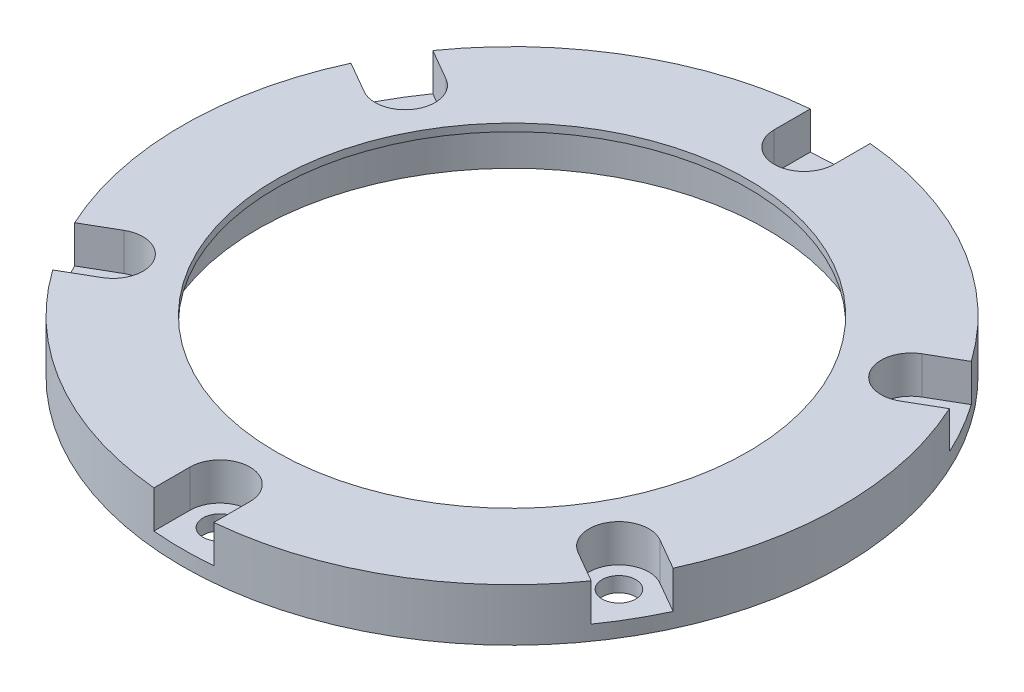
SolidWorks part; units mm, degrees
material "7075-T6, 플레이트 (SS)"
ref_plane "정면" through (0, 0, 0) normal (0, 0, 1) x (1, 0, 0)
ref_plane "윗면" through (0, 0, 0) normal (0, 1, 0) x (1, 0, 0)
ref_plane "우측면" through (0, 0, 0) normal (1, 0, 0) x (0, 0, -1)
sketch "스케치1" plane through (0, 0, 0) normal (0, 1, 0) x (1, 0, 0)
  circle A0 centre (0, 0) radius 44
  circle A1 centre (0, 0) radius 34
  dimension "D1" = 88
  dimension "D2" = 68
extrude "보스-돌출1" add sketch "스케치1" along normal blind 6
sketch "스케치2" plane through (0, 6, 0) normal (0, 1, 0) x (1, 0, 0)
  circle A0 centre (0, 0) radius 31.5
  circle A1 centre (0, 0) radius 44 construction
  circle A2 centre (0, 0) radius 44
  dimension "D1" = 63
extrude "보스-돌출2" add sketch "스케치2" along normal blind 1
sketch "스케치3" plane through (0, 7, 0) normal (0, 1, 0) x (1, 0, 0)
  circle A0 centre (0, 0) radius 39 construction
  point P3 (0, 39)
  dimension "D1" = 78
hole_wizard "M4 육각 소켓 머리 캡 나사용 카운터보어1" positions "스케치4" profile "스케치6" counterbore size "M4" standard "ISO" end condition through all
sketch "스케치4" plane through (0, 7, 0) normal (0, 1, 0) x (1, 0, 0)
  point P0 (0, 39)
sketch "스케치6" plane through (0, 7, -39) normal (1, 0, 0) x (0, 0, 1)
  line L0 (0, 0) -> (0, 7)
  line L1 (0, 7) -> (2.25, 7)
  line L3 (2.25, 7) -> (2.25, 5)
  line L4 (2.25, 5) -> (4, 5)
  line L5 (4, 5) -> (4, 0)
  line L7 (4, 0) -> (0, 0)
  line L11 (0, -6.35) -> (0, 107.95) construction
  dimension "관통 구멍 지름" = 4.5
  dimension "관통 구멍 깊이" = 7
  dimension "카운터보어 지름" = 8
  dimension "카운터보어 깊이" = 5
pattern_circular "원형 패턴1" count 6 over 360 about axis through (0, 0, 0) along (0, 1, 0) of "M4 육각 소켓 머리 캡 나사용 카운터보어1"
fillet "필렛1" [suppressed] radius 0.3
sketch "스케치7" plane through (0, 7, 0) normal (0, 1, 0) x (1, 0, 0)
  line L2 (-4, 39) -> (-4, 44)
  line L3 (-4, 44) -> (4, 44)
  line L4 (4, 39) -> (4, 44)
  circle A0 centre (0, 39) radius 4 construction
  circle A1 centre (0, 39) radius 4 construction
  arc A2 (4, 39) -> (-4, 39) centre (0, 39) ccw
  circle A3 centre (0, 0) radius 44 construction
extrude "컷-돌출1" cut sketch "스케치7" against normal mid plane 10
pattern_circular "원형 패턴2" count 6 over 360 about axis through (0, 0, 0) along (0, 1, 0) of "컷-돌출1"
